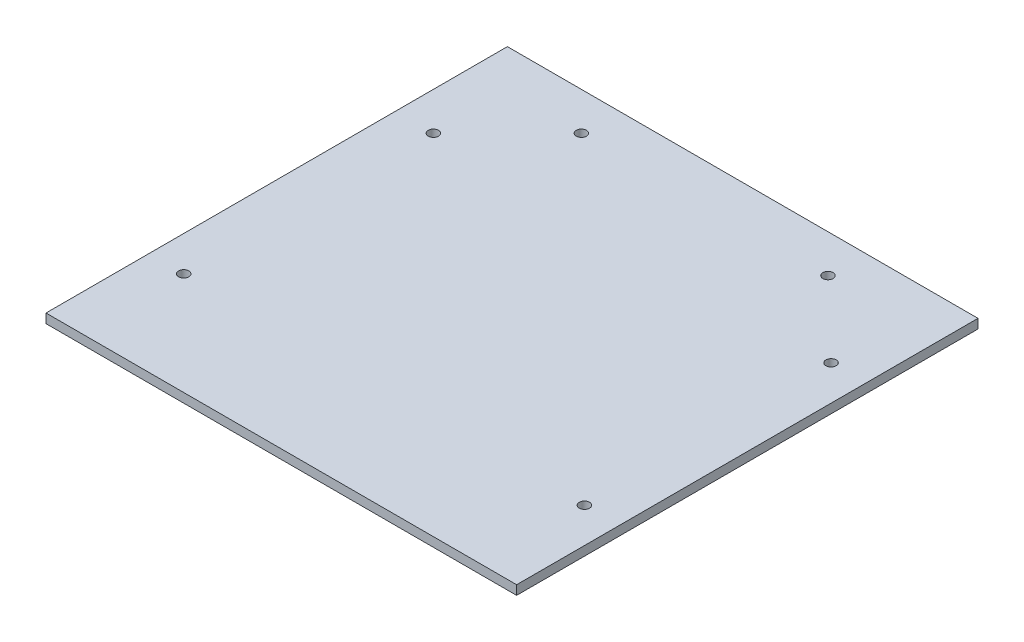
SolidWorks part; units mm, degrees
ref_plane "Front" through (0, 0, 0) normal (0, 0, 1) x (1, 0, 0)
ref_plane "Top" through (0, 0, 0) normal (0, 1, 0) x (1, 0, 0)
ref_plane "Right" through (0, 0, 0) normal (1, 0, 0) x (0, 0, -1)
sketch "Sketch1" plane through (0, 0, 0) normal (0, 1, 0) x (1, 0, 0)
  line L1 (-114.5, -112.25) -> (114.5, -112.25)
  line L2 (-114.5, -112.25) -> (-114.5, 112.25)
  line L3 (-114.5, 112.25) -> (114.5, 112.25)
  line L4 (114.5, -112.25) -> (114.5, 112.25)
  line L5 (-114.5, -112.25) -> (114.5, 112.25) construction
  line L6 (-114.5, 112.25) -> (114.5, -112.25) construction
  point P0 (0, 0)
  dimension "D1" = 229
  dimension "D2" = 224.5
extrude "Boss-Extrude1" add sketch "Sketch1" along normal blind 4.5
sketch "Sketch2" plane through (0, 0, 0) normal (0, -1, 0) x (-1, 0, 0)
  circle A0 centre (97.5, -62.25) radius 2.5
  circle A1 centre (96, 57.75) radius 2.5
  circle A2 centre (60, 93.75) radius 2.5
  circle A3 centre (-60, 93.75) radius 2.5
  circle A4 centre (-97.5, -62.25) radius 2.5
  circle A5 centre (-97.5, 57.75) radius 2.5
extrude "Cut-Extrude1" cut sketch "Sketch2" against normal up to next
